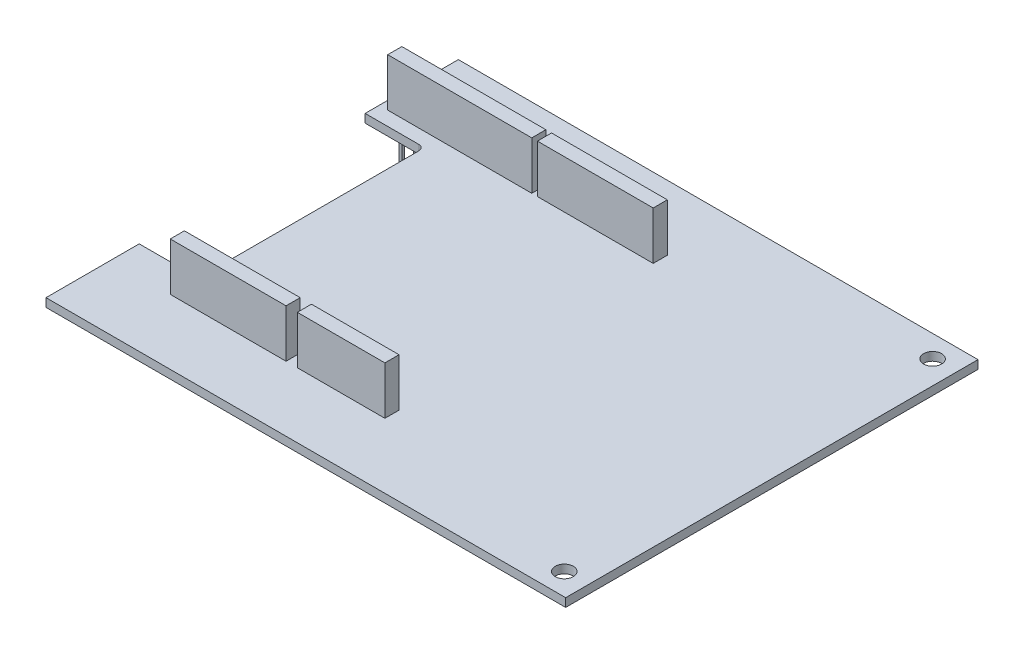
SolidWorks part; units mm, degrees
ref_plane "Płaszczyzna przednia" through (0, 0, 0) normal (0, 0, 1) x (1, 0, 0)
ref_plane "Płaszczyzna górna" through (0, 0, 0) normal (0, 1, 0) x (1, 0, 0)
ref_plane "Płaszczyzna prawa" through (0, 0, 0) normal (1, 0, 0) x (0, 0, -1)
sketch "Szkic1" plane through (0, 0, 0) normal (0, 1, 0) x (1, 0, 0)
  line L0 (-46, 36.5) -> (46, 36.5)
  line L1 (46, 36.5) -> (46, -36.5)
  line L2 (46, -36.5) -> (-46, -36.5)
  line L3 (-46, -36.5) -> (-46, -20)
  line L4 (-46, -20) -> (-36.5, -20)
  line L5 (-35.5, -19) -> (-35.5, 19)
  line L6 (-36.5, 20) -> (-46, 20)
  line L7 (-46, 20) -> (-46, 36.5)
  arc A0 (-36.5, -20) -> (-35.5, -19) centre (-36.5, -19) ccw
  arc A1 (-35.5, 19) -> (-36.5, 20) centre (-36.5, 19) ccw
  circle A2 centre (41.86, 32.6) radius 1.6
  circle A3 centre (41.86, -32.6) radius 1.6
  point P2 (-35.5, 0)
  point P9 (0, 36.5)
  point P19 (0, 0)
  point P20 (38.0278, -29.7732)
  dimension "D7" = 1
  dimension "D8" = 3.2
  dimension "D9" = 2.54
  dimension "D10" = 2.3
  dimension "D11" = 2.3
  dimension "D1" = 92
  dimension "D2" = 73
  dimension "D3" = 40
  dimension "D4" = 16.5
  dimension "D5" = 16.5
  dimension "D6" = 10.5
extrude "Dodanie-wyciągnięcie1" add sketch "Szkic1" along normal blind 1.5
sketch "Szkic2" plane through (0, 1.5, 0) normal (0, 1, 0) x (1, 0, 0)
  line L0 (46, 36.5) -> (-46, 36.5) construction
  line L1 (2.5, -22.5) -> (-13, -22.5)
  line L2 (2.5, -22.5) -> (2.5, -25)
  line L3 (2.5, -25) -> (-13, -25)
  line L4 (-13, -22.5) -> (-13, -25)
  line L5 (-15, -22.5) -> (-35.5, -22.5)
  line L6 (-15, -22.5) -> (-15, -25)
  line L7 (-15, -25) -> (-35.5, -25)
  line L8 (-35.5, -22.5) -> (-35.5, -25)
  line L9 (2.5, 25) -> (-18, 25)
  line L10 (2.5, 25) -> (2.5, 22.5)
  line L11 (2.5, 22.5) -> (-18, 22.5)
  line L12 (-18, 25) -> (-18, 22.5)
  line L13 (-19, 25) -> (-44.5, 25)
  line L14 (-19, 25) -> (-19, 22.5)
  line L15 (-19, 22.5) -> (-44.5, 22.5)
  line L16 (-44.5, 25) -> (-44.5, 22.5)
  line L17 (-46, 36.5) -> (-46, 20) construction
  point P16 (0, 0)
  point P17 (0, 0)
  point P19 (-39.0079, 25.047)
  dimension "D1" = 2.5
  dimension "D2" = 15.5
  dimension "D3" = 2.5
  dimension "D4" = 20.5
  dimension "D5" = 2.5
  dimension "D6" = 20.5
  dimension "D7" = 2.5
  dimension "D8" = 25.5
  dimension "D9" = 50
  dimension "D10" = 1
  dimension "D11" = 2
  dimension "D12" = 11.5
  dimension "D13" = 1.5
extrude "Dodanie-wyciągnięcie2" add sketch "Szkic2" along normal blind 8.5
sketch "Szkic3" plane through (0, 0, 0) normal (0, -1, 0) x (1, 0, 0)
  line L0 (-40.9444, -24) -> (-40.9444, -23.5)
  line L1 (-15, 25) -> (-15, 22.5) construction
  line L2 (-15, 22.5) -> (-35.5, 22.5) construction
  line L3 (-35.5, 22.5) -> (-35.5, 25) construction
  line L4 (-35.5, 25) -> (-15, 25) construction
  line L5 (2.5, 25) -> (2.5, 22.5) construction
  line L6 (2.5, 22.5) -> (-13, 22.5) construction
  line L7 (-13, 22.5) -> (-13, 25) construction
  line L8 (-13, 25) -> (2.5, 25) construction
  line L9 (2.5, -22.5) -> (2.5, -25) construction
  line L10 (2.5, -25) -> (-18, -25) construction
  line L11 (-18, -25) -> (-18, -22.5) construction
  line L12 (-18, -22.5) -> (2.5, -22.5) construction
  line L13 (-19, -22.5) -> (-19, -25) construction
  line L14 (-19, -25) -> (-44.5, -25) construction
  line L15 (-44.5, -25) -> (-44.5, -22.5) construction
  line L16 (-44.5, -22.5) -> (-19, -22.5) construction
  line L17 (-15, 25) -> (-15, 22.5) construction
  line L18 (-15, 22.5) -> (-35.5, 22.5) construction
  line L19 (-35.5, 22.5) -> (-35.5, 25) construction
  line L20 (-35.5, 25) -> (-15, 25) construction
  line L21 (2.5, 25) -> (2.5, 22.5) construction
  line L22 (2.5, 22.5) -> (-13, 22.5) construction
  line L23 (-13, 22.5) -> (-13, 25) construction
  line L24 (-13, 25) -> (2.5, 25) construction
  line L25 (2.5, -22.5) -> (2.5, -25) construction
  line L26 (2.5, -25) -> (-18, -25) construction
  line L27 (-18, -25) -> (-18, -22.5) construction
  line L28 (-18, -22.5) -> (2.5, -22.5) construction
  line L29 (-19, -22.5) -> (-19, -25) construction
  line L30 (-19, -25) -> (-44.5, -25) construction
  line L31 (-44.5, -25) -> (-44.5, -22.5) construction
  line L32 (-44.5, -22.5) -> (-19, -22.5) construction
  line L33 (-16, 24) -> (-16, 23.5)
  line L34 (-16, 23.5) -> (-34.5, 23.5) construction
  line L35 (-34.5, 23.5) -> (-34.5, 24)
  line L36 (-34.5, 24) -> (-16, 24) construction
  line L37 (1.5, 24) -> (1.5, 23.5) construction
  line L38 (1.5, 23.5) -> (-12, 23.5) construction
  line L39 (-12, 23.5) -> (-12, 24)
  line L40 (-12, 24) -> (1.5, 24) construction
  line L41 (1.5, -23.5) -> (1.5, -24)
  line L42 (1.5, -24) -> (-17, -24) construction
  line L43 (-17, -24) -> (-17, -23.5) construction
  line L44 (-17, -23.5) -> (1.5, -23.5) construction
  line L45 (-20, -23.5) -> (-20, -24)
  line L46 (-20, -24) -> (-43.5, -24) construction
  line L47 (-43.5, -24) -> (-43.5, -23.5) construction
  line L48 (-43.5, -23.5) -> (-20, -23.5) construction
  line L49 (-31.9286, 23.5002) -> (-31.9286, 24.0002)
  line L50 (-34.5, 23.5) -> (-34, 23.5)
  line L51 (-34.5, 23.5) -> (-34.5, 24)
  line L52 (-34.5, 24) -> (-34, 24)
  line L53 (-34, 23.5) -> (-34, 24)
  line L54 (-31.9286, 23.5002) -> (-31.4286, 23.5002)
  line L55 (-31.4286, 23.5002) -> (-31.4286, 24.0002)
  line L56 (-31.9286, 24.0002) -> (-31.4286, 24.0002)
  line L57 (-29.3571, 23.5003) -> (-29.3571, 24.0003)
  line L58 (-29.3571, 23.5003) -> (-28.8571, 23.5003)
  line L59 (-28.8571, 23.5003) -> (-28.8571, 24.0003)
  line L60 (-29.3571, 24.0003) -> (-28.8571, 24.0003)
  line L61 (-26.7857, 23.5005) -> (-26.7857, 24.0005)
  line L62 (-26.7857, 23.5005) -> (-26.2857, 23.5005)
  line L63 (-26.2857, 23.5005) -> (-26.2857, 24.0005)
  line L64 (-26.7857, 24.0005) -> (-26.2857, 24.0005)
  line L65 (-24.2143, 23.5007) -> (-24.2143, 24.0007)
  line L66 (-24.2143, 23.5007) -> (-23.7143, 23.5007)
  line L67 (-23.7143, 23.5007) -> (-23.7143, 24.0007)
  line L68 (-24.2143, 24.0007) -> (-23.7143, 24.0007)
  line L69 (-21.6429, 23.5008) -> (-21.6429, 24.0008)
  line L70 (-21.6429, 23.5008) -> (-21.1429, 23.5008)
  line L71 (-21.1429, 23.5008) -> (-21.1429, 24.0008)
  line L72 (-21.6429, 24.0008) -> (-21.1429, 24.0008)
  line L73 (-19.0714, 23.501) -> (-19.0714, 24.001)
  line L74 (-19.0714, 23.501) -> (-18.5714, 23.501)
  line L75 (-18.5714, 23.501) -> (-18.5714, 24.001)
  line L76 (-19.0714, 24.001) -> (-18.5714, 24.001)
  line L77 (-16.5, 23.5012) -> (-16.5, 24.0012)
  line L78 (-16.5, 23.5012) -> (-16, 23.5012)
  line L79 (-16, 23.5012) -> (-16, 24.0012)
  line L80 (-16.5, 24.0012) -> (-16, 24.0012)
  line L81 (-9.4, 23.5) -> (-9.4, 24)
  line L82 (-12, 23.5) -> (-11.5, 23.5)
  line L83 (-12, 23.5) -> (-12, 24)
  line L84 (-12, 24) -> (-11.5, 24)
  line L85 (-11.5, 23.5) -> (-11.5, 24)
  line L86 (-9.4, 23.5) -> (-8.9, 23.5)
  line L87 (-8.9, 23.5) -> (-8.9, 24)
  line L88 (-9.4, 24) -> (-8.9, 24)
  line L89 (-6.8, 23.5) -> (-6.8, 24)
  line L90 (-6.8, 23.5) -> (-6.3, 23.5)
  line L91 (-6.3, 23.5) -> (-6.3, 24)
  line L92 (-6.8, 24) -> (-6.3, 24)
  line L93 (-4.2, 23.5) -> (-4.2, 24)
  line L94 (-4.2, 23.5) -> (-3.7, 23.5)
  line L95 (-3.7, 23.5) -> (-3.7, 24)
  line L96 (-4.2, 24) -> (-3.7, 24)
  line L97 (-1.6, 23.5) -> (-1.6, 24)
  line L98 (-1.6, 23.5) -> (-1.1, 23.5)
  line L99 (-1.1, 23.5) -> (-1.1, 24)
  line L100 (-1.6, 24) -> (-1.1, 24)
  line L101 (1, 23.5) -> (1, 24)
  line L102 (1, 23.5) -> (1.5, 23.5)
  line L103 (1.5, 23.5) -> (1.5, 24)
  line L104 (1, 24) -> (1.5, 24)
  line L105 (-40.9444, -24) -> (-40.4444, -24)
  line L106 (-43.5, -24) -> (-43, -24)
  line L107 (-43.5, -24) -> (-43.5, -23.5)
  line L108 (-43.5, -23.5) -> (-43, -23.5)
  line L109 (-43, -24) -> (-43, -23.5)
  line L110 (-17, -24) -> (-16.5, -24)
  line L111 (-17, -24) -> (-17, -23.5)
  line L112 (-17, -23.5) -> (-16.5, -23.5)
  line L113 (-16.5, -24) -> (-16.5, -23.5)
  line L114 (-40.4444, -24) -> (-40.4444, -23.5)
  line L115 (-40.9444, -23.5) -> (-40.4444, -23.5)
  line L116 (-38.3889, -24) -> (-38.3889, -23.5)
  line L117 (-38.3889, -24) -> (-37.8889, -24)
  line L118 (-37.8889, -24) -> (-37.8889, -23.5)
  line L119 (-38.3889, -23.5) -> (-37.8889, -23.5)
  line L120 (-35.8333, -24) -> (-35.8333, -23.5)
  line L121 (-35.8333, -24) -> (-35.3333, -24)
  line L122 (-35.3333, -24) -> (-35.3333, -23.5)
  line L123 (-35.8333, -23.5) -> (-35.3333, -23.5)
  line L124 (-33.2778, -24) -> (-33.2778, -23.5)
  line L125 (-33.2778, -24) -> (-32.7778, -24)
  line L126 (-32.7778, -24) -> (-32.7778, -23.5)
  line L127 (-33.2778, -23.5) -> (-32.7778, -23.5)
  line L128 (-30.7222, -24) -> (-30.7222, -23.5)
  line L129 (-30.7222, -24) -> (-30.2222, -24)
  line L130 (-30.2222, -24) -> (-30.2222, -23.5)
  line L131 (-30.7222, -23.5) -> (-30.2222, -23.5)
  line L132 (-28.1667, -24) -> (-28.1667, -23.5)
  line L133 (-28.1667, -24) -> (-27.6667, -24)
  line L134 (-27.6667, -24) -> (-27.6667, -23.5)
  line L135 (-28.1667, -23.5) -> (-27.6667, -23.5)
  line L136 (-25.6111, -24) -> (-25.6111, -23.5)
  line L137 (-25.6111, -24) -> (-25.1111, -24)
  line L138 (-25.1111, -24) -> (-25.1111, -23.5)
  line L139 (-25.6111, -23.5) -> (-25.1111, -23.5)
  line L140 (-23.0556, -24) -> (-23.0556, -23.5)
  line L141 (-23.0556, -24) -> (-22.5556, -24)
  line L142 (-22.5556, -24) -> (-22.5556, -23.5)
  line L143 (-23.0556, -23.5) -> (-22.5556, -23.5)
  line L144 (-20.5, -24) -> (-20.5, -23.5)
  line L145 (-20.5, -24) -> (-20, -24)
  line L146 (-20, -24) -> (-20, -23.5)
  line L147 (-20.5, -23.5) -> (-20, -23.5)
  line L148 (-14.4286, -24) -> (-13.9286, -24)
  line L149 (-14.4286, -24) -> (-14.4286, -23.5)
  line L150 (-13.9286, -24) -> (-13.9286, -23.5)
  line L151 (-14.4286, -23.5) -> (-13.9286, -23.5)
  line L152 (-11.8571, -24) -> (-11.3571, -24)
  line L153 (-11.8571, -24) -> (-11.8571, -23.5)
  line L154 (-11.3571, -24) -> (-11.3571, -23.5)
  line L155 (-11.8571, -23.5) -> (-11.3571, -23.5)
  line L156 (-9.2857, -24) -> (-8.7857, -24)
  line L157 (-9.2857, -24) -> (-9.2857, -23.5)
  line L158 (-8.7857, -24) -> (-8.7857, -23.5)
  line L159 (-9.2857, -23.5) -> (-8.7857, -23.5)
  line L160 (-6.7143, -24) -> (-6.2143, -24)
  line L161 (-6.7143, -24) -> (-6.7143, -23.5)
  line L162 (-6.2143, -24) -> (-6.2143, -23.5)
  line L163 (-6.7143, -23.5) -> (-6.2143, -23.5)
  line L164 (-4.1429, -24) -> (-3.6429, -24)
  line L165 (-4.1429, -24) -> (-4.1429, -23.5)
  line L166 (-3.6429, -24) -> (-3.6429, -23.5)
  line L167 (-4.1429, -23.5) -> (-3.6429, -23.5)
  line L168 (-1.5714, -24) -> (-1.0714, -24)
  line L169 (-1.5714, -24) -> (-1.5714, -23.5)
  line L170 (-1.0714, -24) -> (-1.0714, -23.5)
  line L171 (-1.5714, -23.5) -> (-1.0714, -23.5)
  line L172 (1, -24) -> (1.5, -24)
  line L173 (1, -24) -> (1, -23.5)
  line L174 (1.5, -24) -> (1.5, -23.5)
  line L175 (1, -23.5) -> (1.5, -23.5)
  point P35 (-16.25, 23.7512)
  point P67 (1.25, 23.75)
  point P68 (1.5, 23.75)
  point P95 (-20.25, -23.75)
  point P96 (1.5, -23.75)
  point P97 (-20, -23.75)
  point P98 (1.25, -23.75)
  dimension "D3" = 0.25
  dimension "D4" = 0.2488
  dimension "D5" = 0.25
  dimension "D6" = 0.25
  dimension "D8" = 0.25
  dimension "D9" = 0.25
  dimension "D10" = 0.25
  dimension "D11" = 0.25
  dimension "D1" = 1
  dimension "D2" = 8
  dimension "D7" = 6
  dimension "D12" = 10
  dimension "D13" = 8
extrude "Dodanie-wyciągnięcie3" add sketch "Szkic3" along normal blind 8.5 contours L106 L109 L108 L107 | L115 L0 L105 L114 | L119 L116 L117 L118 | L123 L120 L121 L122 | L127 L124 L125 L126 | L131 L128 L129 L130 | L135 L132 L133 L134 | L139 L136 L137 L138 | L143 L140 L141 L142 | L147 L144 L145 L45 | L110 L113 L112 L111 | L151 L149 L148 L150 | L155 L153 L152 L154 | L159 L157 L156 L158 | L163 L161 L160 L162 | L167 L165 L164 L166 | L171 L169 L168 L170 | L175 L173 L172 L41 | L50 L53 L52 L35 | L56 L49 L54 L55 | L60 L57 L58 L59 | L64 L61 L62 L63 | L68 L65 L66 L67 | L72 L69 L70 L71 | L76 L73 L74 L75 | L80 L77 L78 L33 L79 | L82 L85 L84 L39 | L88 L81 L86 L87 | L92 L89 L90 L91 | L96 L93 L94 L95 | L100 L97 L98 L99 | L104 L101 L102 L103
equation "\"D5@Szkic3\"=\"D6@Szkic3\""
equation "\"D8@Szkic3\"=\"D9@Szkic3\""
equation "\"D10@Szkic3\"=\"D11@Szkic3\""
